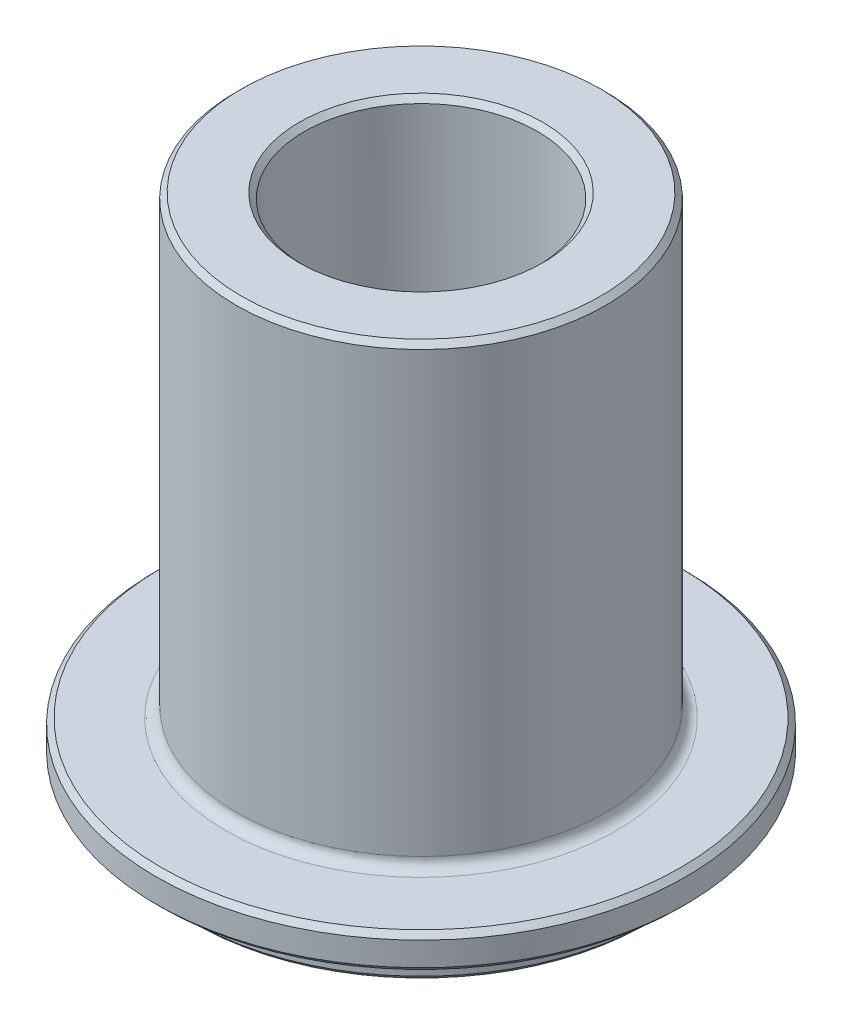
SolidWorks part; units mm, degrees
ref_plane "Front Plane" through (0, 0, 0) normal (0, 0, 1) x (1, 0, 0)
ref_plane "Top Plane" through (0, 0, 0) normal (0, 1, 0) x (1, 0, 0)
ref_plane "Right Plane" through (0, 0, 0) normal (1, 0, 0) x (0, 0, -1)
sketch "Sketch1" plane through (0, 0, 0) normal (0, 0, 1) x (1, 0, 0)
  line L0 (0, 0) -> (0, 49.2)
  line L1 (12.3346, 0) -> (21.75, 0)
  line L2 (21.75, 0) -> (21.75, 3)
  line L3 (21.75, 3) -> (25, 3)
  line L4 (25, 3) -> (25, 6.25)
  line L5 (25, 6.25) -> (17.45, 6.25)
  line L6 (17.45, 6.25) -> (17.45, 49.2)
  line L7 (17.45, 49.2) -> (11, 49.2)
  line L8 (17.45, 49.2) -> (11, 49.2)
  line L9 (11, 49.2) -> (11, 33.23)
  line L10 (12.3346, 0) -> (12.3346, 25.3)
  line L11 (12.3346, 25.3) -> (1.493, 25.3)
  line L12 (1.493, 25.3) -> (1.493, 27.8)
  line L13 (1.493, 27.8) -> (11, 33.23)
  dimension "D1" = 49.2
  dimension "D2" = 17.45
  dimension "D3" = 6.45
  dimension "D4" = 15.97
  dimension "D5" = 25.3
  dimension "D6" = 21.75
  dimension "D7" = 25
  dimension "D8" = 3
  dimension "D9" = 3.25
  dimension "D10" = 2.5
revolve "Revolve1" add sketch "Sketch1" angle 360 about L0
chamfer "Chamfer1" distance 0.5 angle 45 7 edges at (0, 6.25, -25) (0, 3, -25) (0, 0, -21.75) (0, 0, -12.3346) (0, 25.3, -1.493) (0, 49.2, -11) (0, 49.2, -17.45)
fillet "Fillet1" radius 1 1 edges at (0, 6.25, -17.45)
chamfer "Chamfer2" distance 0.5 angle 45 1 edges at (0, 25.3, -12.3346)
equation "\"`1mm\"=10"
